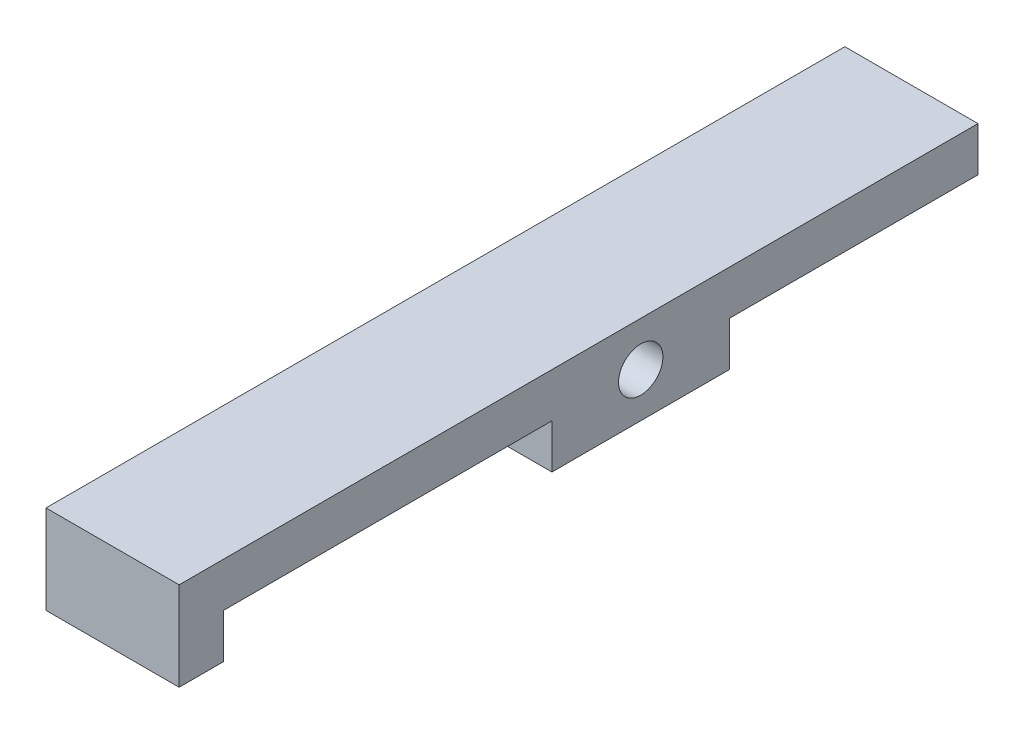
SolidWorks part; units mm, degrees
material "6061 Alloy"
ref_plane "Front Plane" through (0, 0, 0) normal (0, 0, 1) x (1, 0, 0)
ref_plane "Top Plane" through (0, 0, 0) normal (0, 1, 0) x (1, 0, 0)
ref_plane "Right Plane" through (0, 0, 0) normal (1, 0, 0) x (0, 0, -1)
sketch "Sketch1" plane through (0, 0, 0) normal (1, 0, 0) x (0, 0, -1)
  line L0 (0, 1.5875) -> (0, -1.5875)
  line L1 (0, -1.5875) -> (-17.78, -1.5875)
  line L2 (-53.975, -1.5875) -> (-53.975, -4.7625)
  line L3 (-53.975, -4.7625) -> (-57.15, -4.7625)
  line L4 (-57.15, -4.7625) -> (-57.15, 1.5875)
  line L5 (-57.15, 1.5875) -> (0, 1.5875)
  line L6 (-30.48, -1.5875) -> (-53.975, -1.5875)
  line L8 (-30.48, -1.5875) -> (-30.48, -4.7625)
  line L9 (-30.48, -4.7625) -> (-17.78, -4.7625)
  line L10 (-17.78, -1.5875) -> (-17.78, -4.7625)
  circle A0 centre (-24.13, -1.5875) radius 1.5875
  point P14 (-24.13, -4.7625)
  dimension "D6" = 3.175
  dimension "D1" = 3.175
  dimension "D2" = 3.175
  dimension "D3" = 6.35
  dimension "D4" = 57.15
  dimension "D5" = 3.175
  dimension "D7" = 12.7
  dimension "D8" = 17.78
extrude "Boss-Extrude1" add sketch "Sketch1" along normal blind 9.525
ref_plane "Center Plane" through (4.7625, 0, 0) normal (1, 0, 0) x (0, 0, -1)
